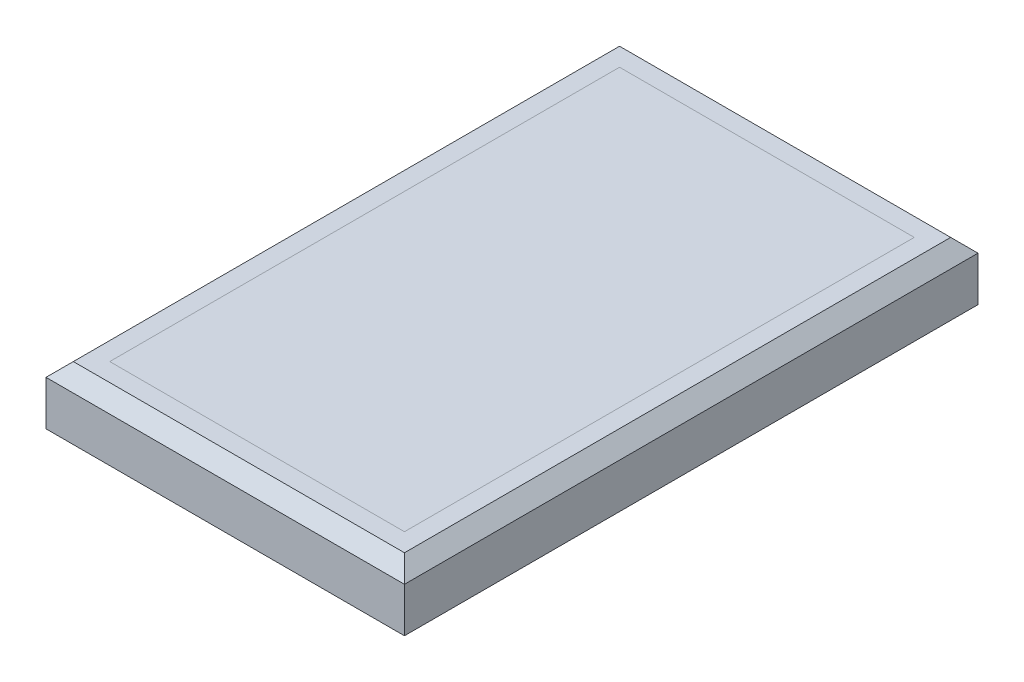
SolidWorks part; units mm, degrees
ref_plane "Front" through (0, 0, 0) normal (0, 0, 1) x (1, 0, 0)
ref_plane "Top" through (0, 0, 0) normal (0, 1, 0) x (1, 0, 0)
ref_plane "Right" through (0, 0, 0) normal (1, 0, 0) x (0, 0, -1)
sketch "Sketch1" plane through (0, 0, 0) normal (0, 1, 0) x (1, 0, 0)
  line L0 (-125, 200) -> (125, -200) construction
  line L1 (-125, 200) -> (125, 200)
  line L2 (-125, 200) -> (-125, -200)
  line L3 (-125, -200) -> (125, -200)
  line L4 (125, 200) -> (125, -200)
  dimension "D1" = 250
  dimension "D2" = 400
extrude "Boss-Extrude1" add sketch "Sketch1" along normal blind 40.64
sketch "Sketch2" plane through (0, 40.64, 0) normal (0, 1, 0) x (1, 0, 0)
  line L8 (-102.775, 177.775) -> (-102.775, -177.775)
  line L9 (-102.775, -177.775) -> (102.775, -177.775)
  line L10 (102.775, -177.775) -> (102.775, 177.775)
  line L11 (102.775, 177.775) -> (-102.775, 177.775)
  line L12 (-102.775, 177.775) -> (-102.775, -177.775)
  line L13 (-102.775, -177.775) -> (102.775, -177.775)
  line L14 (102.775, -177.775) -> (102.775, 177.775)
  line L15 (102.775, 177.775) -> (-102.775, 177.775)
  dimension "D1" = 22.225
extrude "Cut-Extrude1" cut sketch "Sketch2" against normal blind 38.1
chamfer "Chamfer1" distance 9.525 angle 45 4 edges at (0, 40.64, -200) (125, 40.64, 0) (0, 40.64, 200) (-125, 40.64, 0)
ref_plane "Plane1" through (0, 37.465, 0) normal (0, 1, 0) x (1, 0, 0)
sketch "Sketch3" plane through (0, 37.465, 0) normal (0, 1, 0) x (1, 0, 0)
  line L0 (0, 177.775) -> (0, -177.775) construction
  line L1 (102.775, 177.775) -> (-102.775, 177.775) construction
  line L2 (-102.775, -177.775) -> (102.775, -177.775) construction
  line L3 (102.775, -177.775) -> (102.775, 177.775) construction
  line L4 (-102.775, 177.775) -> (-102.775, -177.775) construction
  line L5 (-102.775, -177.775) -> (102.775, -177.775)
  line L6 (102.775, -177.775) -> (102.775, 177.775)
  line L7 (-102.775, 177.775) -> (-102.775, -177.775)
  line L8 (102.775, 177.775) -> (-102.775, 177.775)
extrude "Boss-Extrude2" add sketch "Sketch3" against normal blind 3.175 separate body
sketch "Sketch4" plane through (0, 37.465, 0) normal (0, 1, 0) x (1, 0, 0)
  line L0 (0, 177.775) -> (0, -177.775) construction
  line L1 (102.775, 177.775) -> (-102.775, 177.775) construction
  line L2 (-102.775, -177.775) -> (102.775, -177.775) construction
  line L3 (1.5875, 177.775) -> (1.5875, -177.775)
  line L4 (-1.5875, 177.775) -> (-1.5875, -177.775)
  line L5 (71.1625, 177.775) -> (67.9875, 177.775)
  line L6 (-71.1625, -177.775) -> (-67.9875, -177.775)
  line L7 (36.375, 177.775) -> (36.375, -177.775)
  line L8 (33.2, 177.775) -> (33.2, -177.775)
  line L9 (71.1625, 177.775) -> (71.1625, -177.775)
  line L10 (67.9875, 177.775) -> (67.9875, -177.775)
  line L11 (-33.2, 177.775) -> (-33.2, -177.775)
  line L12 (-36.375, 177.775) -> (-36.375, -177.775)
  line L13 (-67.9875, 177.775) -> (-67.9875, -177.775)
  line L14 (-71.1625, 177.775) -> (-71.1625, -177.775)
  line L15 (102.775, 177.775) -> (-102.775, 177.775) construction
  line L16 (1.5875, 0) -> (33.2, 0) construction
  line L17 (36.375, 0) -> (67.9875, 0) construction
  line L18 (71.1625, 0) -> (102.775, 0) construction
  line L19 (102.775, -177.775) -> (102.775, 177.775) construction
  line L20 (-1.5875, 0) -> (-33.2, 0) construction
  line L21 (-36.375, 0) -> (-67.9875, 0) construction
  line L22 (-71.1625, 0) -> (-102.775, 0) construction
  line L23 (-102.775, 177.775) -> (-102.775, -177.775) construction
  line L24 (36.375, 177.775) -> (33.2, 177.775)
  line L25 (1.5875, 177.775) -> (-1.5875, 177.775)
  line L26 (-33.2, 177.775) -> (-36.375, 177.775)
  line L27 (-67.9875, 177.775) -> (-71.1625, 177.775)
  line L28 (67.9875, -177.775) -> (71.1625, -177.775)
  line L29 (33.2, -177.775) -> (36.375, -177.775)
  line L30 (-1.5875, -177.775) -> (1.5875, -177.775)
  line L31 (-36.375, -177.775) -> (-33.2, -177.775)
  dimension "D1" = 3.175
extrude "Cut-Extrude2" cut sketch "Sketch4" against normal blind 7.62
sketch "Sketch5" plane through (0, 37.465, 0) normal (0, 1, 0) x (1, 0, 0)
  line L0 (-102.775, 0) -> (102.775, 0) construction
  line L1 (-102.775, 177.775) -> (-102.775, -177.775) construction
  line L2 (102.775, -177.775) -> (102.775, 177.775) construction
  line L3 (-102.775, 1.5875) -> (102.775, 1.5875)
  line L4 (102.775, -177.775) -> (102.775, 177.775) construction
  line L5 (-102.775, 177.775) -> (-102.775, -177.775) construction
  line L6 (-102.775, -1.5875) -> (102.775, -1.5875)
  line L7 (-102.775, -34.285) -> (102.775, -34.285)
  line L8 (-102.775, -37.46) -> (102.775, -37.46)
  line L9 (-102.775, -70.1575) -> (102.775, -70.1575)
  line L10 (-102.775, -73.3325) -> (102.775, -73.3325)
  line L11 (-102.775, -106.03) -> (102.775, -106.03)
  line L12 (-102.775, -109.205) -> (102.775, -109.205)
  line L13 (-102.775, -141.9025) -> (102.775, -141.9025)
  line L14 (-102.775, -145.0775) -> (102.775, -145.0775)
  line L15 (-102.775, 37.46) -> (102.775, 37.46)
  line L16 (-102.775, 34.285) -> (102.775, 34.285)
  line L17 (-102.775, 73.3325) -> (102.775, 73.3325)
  line L18 (-102.775, 70.1575) -> (102.775, 70.1575)
  line L19 (-102.775, 109.205) -> (102.775, 109.205)
  line L20 (-102.775, 106.03) -> (102.775, 106.03)
  line L21 (-102.775, 145.0775) -> (102.775, 145.0775)
  line L22 (-102.775, 141.9025) -> (102.775, 141.9025)
  line L23 (102.775, -145.0775) -> (102.775, -141.9025)
  line L24 (-102.775, 145.0775) -> (-102.775, 141.9025)
  line L25 (-102.775, 109.205) -> (-102.775, 106.03)
  line L26 (102.775, 141.9025) -> (102.775, 145.0775)
  line L27 (102.775, 106.03) -> (102.775, 109.205)
  line L28 (-102.775, 73.3325) -> (-102.775, 70.1575)
  line L29 (-102.775, 37.46) -> (-102.775, 34.285)
  line L30 (102.775, 70.1575) -> (102.775, 73.3325)
  line L31 (102.775, 34.285) -> (102.775, 37.46)
  line L32 (-102.775, 1.5875) -> (-102.775, -1.5875)
  line L33 (-102.775, -70.1575) -> (-102.775, -73.3325)
  line L34 (102.775, -37.46) -> (102.775, -34.285)
  line L35 (-102.775, -106.03) -> (-102.775, -109.205)
  line L36 (102.775, -73.3325) -> (102.775, -70.1575)
  line L37 (102.775, -109.205) -> (102.775, -106.03)
  line L38 (-102.775, -141.9025) -> (-102.775, -145.0775)
  line L39 (102.775, 1.5875) -> (102.775, -1.5875)
  line L40 (0, -1.5875) -> (0, -34.285) construction
  line L41 (-102.775, -34.285) -> (-102.775, -37.46)
  line L42 (0, -37.46) -> (0, -70.1575) construction
  line L43 (0, -73.3325) -> (0, -106.03) construction
  line L44 (0, -109.205) -> (0, -141.9025) construction
  line L45 (0, -145.0775) -> (0, -177.775) construction
  line L46 (-102.775, -177.775) -> (102.775, -177.775) construction
  line L47 (0, 1.5875) -> (0, 34.285) construction
  line L48 (0, 37.46) -> (0, 70.1575) construction
  line L49 (0, 73.3325) -> (0, 106.03) construction
  line L50 (0, 109.205) -> (0, 141.9025) construction
  line L51 (0, 145.0775) -> (0, 177.775) construction
  line L52 (102.775, 177.775) -> (-102.775, 177.775) construction
  dimension "D1" = 3.175
extrude "Cut-Extrude3" cut sketch "Sketch5" against normal blind 7.62
sketch "Sketch6" plane through (0, 37.465, 0) normal (0, 1, 0) x (1, 0, 0)
  line L0 (-71.1625, -109.205) -> (-102.775, -109.205) construction
  line L1 (-102.775, -141.9025) -> (-102.775, -145.0775)
  line L2 (-102.775, -141.9025) -> (-71.1625, -141.9025) construction
  line L3 (-71.1625, -141.9025) -> (-71.1625, -109.205) construction
  line L4 (-71.1625, -145.0775) -> (-102.775, -145.0775) construction
  line L5 (-102.775, -106.03) -> (-102.775, -109.205)
  line L6 (-102.775, -70.1575) -> (-102.775, -73.3325)
  line L7 (-71.1625, -177.775) -> (-71.1625, -145.0775) construction
  line L8 (-36.375, -145.0775) -> (-67.9875, -145.0775) construction
  line L9 (-67.9875, -145.0775) -> (-67.9875, -177.775) construction
  line L10 (-102.775, -34.285) -> (-102.775, -37.46)
  line L11 (-36.375, -177.775) -> (-36.375, -145.0775) construction
  line L12 (-36.375, -109.205) -> (-67.9875, -109.205) construction
  line L13 (-67.9875, -109.205) -> (-67.9875, -141.9025) construction
  line L14 (-67.9875, -141.9025) -> (-36.375, -141.9025) construction
  line L15 (-36.375, -141.9025) -> (-36.375, -109.205) construction
  line L16 (-1.5875, -109.205) -> (-33.2, -109.205) construction
  line L17 (-33.2, -109.205) -> (-33.2, -141.9025) construction
  line L18 (-33.2, -141.9025) -> (-1.5875, -141.9025) construction
  line L19 (-1.5875, -141.9025) -> (-1.5875, -109.205) construction
  line L20 (-1.5875, -145.0775) -> (-33.2, -145.0775) construction
  line L21 (-33.2, -145.0775) -> (-33.2, -177.775) construction
  line L22 (-102.775, 1.5875) -> (-102.775, -1.5875)
  line L23 (-1.5875, -177.775) -> (-1.5875, -145.0775) construction
  line L24 (33.2, -145.0775) -> (1.5875, -145.0775) construction
  line L25 (1.5875, -145.0775) -> (1.5875, -177.775) construction
  line L26 (-102.775, 37.46) -> (-102.775, 34.285)
  line L27 (33.2, -177.775) -> (33.2, -145.0775) construction
  line L28 (33.2, -109.205) -> (1.5875, -109.205) construction
  line L29 (1.5875, -109.205) -> (1.5875, -141.9025) construction
  line L30 (1.5875, -141.9025) -> (33.2, -141.9025) construction
  line L31 (33.2, -141.9025) -> (33.2, -109.205) construction
  line L32 (67.9875, -109.205) -> (36.375, -109.205) construction
  line L33 (36.375, -109.205) -> (36.375, -141.9025) construction
  line L34 (36.375, -141.9025) -> (67.9875, -141.9025) construction
  line L35 (67.9875, -141.9025) -> (67.9875, -109.205) construction
  line L36 (67.9875, -145.0775) -> (36.375, -145.0775) construction
  line L37 (36.375, -145.0775) -> (36.375, -177.775) construction
  line L38 (-102.775, 73.3325) -> (-102.775, 70.1575)
  line L39 (67.9875, -177.775) -> (67.9875, -145.0775) construction
  line L40 (102.775, -145.0775) -> (71.1625, -145.0775) construction
  line L41 (71.1625, -145.0775) -> (71.1625, -177.775) construction
  line L42 (-102.775, 109.205) -> (-102.775, 106.03)
  line L43 (-67.9875, 177.775) -> (-71.1625, 177.775)
  line L44 (102.775, -109.205) -> (71.1625, -109.205) construction
  line L45 (71.1625, -109.205) -> (71.1625, -141.9025) construction
  line L46 (71.1625, -141.9025) -> (102.775, -141.9025) construction
  line L47 (-33.2, 177.775) -> (-36.375, 177.775)
  line L48 (102.775, -73.3325) -> (71.1625, -73.3325) construction
  line L49 (71.1625, -73.3325) -> (71.1625, -106.03) construction
  line L50 (71.1625, -106.03) -> (102.775, -106.03) construction
  line L51 (1.5875, 177.775) -> (-1.5875, 177.775)
  line L52 (67.9875, -73.3325) -> (36.375, -73.3325) construction
  line L53 (36.375, -73.3325) -> (36.375, -106.03) construction
  line L54 (36.375, -106.03) -> (67.9875, -106.03) construction
  line L55 (67.9875, -106.03) -> (67.9875, -73.3325) construction
  line L56 (33.2, -73.3325) -> (1.5875, -73.3325) construction
  line L57 (1.5875, -73.3325) -> (1.5875, -106.03) construction
  line L58 (1.5875, -106.03) -> (33.2, -106.03) construction
  line L59 (33.2, -106.03) -> (33.2, -73.3325) construction
  line L60 (-1.5875, -73.3325) -> (-33.2, -73.3325) construction
  line L61 (-33.2, -73.3325) -> (-33.2, -106.03) construction
  line L62 (-33.2, -106.03) -> (-1.5875, -106.03) construction
  line L63 (-1.5875, -106.03) -> (-1.5875, -73.3325) construction
  line L64 (-36.375, -73.3325) -> (-67.9875, -73.3325) construction
  line L65 (-67.9875, -73.3325) -> (-67.9875, -106.03) construction
  line L66 (-67.9875, -106.03) -> (-36.375, -106.03) construction
  line L67 (-36.375, -106.03) -> (-36.375, -73.3325) construction
  line L68 (-71.1625, -73.3325) -> (-102.775, -73.3325) construction
  line L69 (36.375, 177.775) -> (33.2, 177.775)
  line L70 (-102.775, -106.03) -> (-71.1625, -106.03) construction
  line L71 (-71.1625, -106.03) -> (-71.1625, -73.3325) construction
  line L72 (-71.1625, -37.46) -> (-102.775, -37.46) construction
  line L73 (102.775, 141.9025) -> (102.775, 145.0775)
  line L74 (-102.775, -70.1575) -> (-71.1625, -70.1575) construction
  line L75 (-71.1625, -70.1575) -> (-71.1625, -37.46) construction
  line L76 (-36.375, -37.46) -> (-67.9875, -37.46) construction
  line L77 (-67.9875, -37.46) -> (-67.9875, -70.1575) construction
  line L78 (-67.9875, -70.1575) -> (-36.375, -70.1575) construction
  line L79 (-36.375, -70.1575) -> (-36.375, -37.46) construction
  line L80 (-1.5875, -37.46) -> (-33.2, -37.46) construction
  line L81 (-33.2, -37.46) -> (-33.2, -70.1575) construction
  line L82 (-33.2, -70.1575) -> (-1.5875, -70.1575) construction
  line L83 (-1.5875, -70.1575) -> (-1.5875, -37.46) construction
  line L84 (33.2, -37.46) -> (1.5875, -37.46) construction
  line L85 (1.5875, -37.46) -> (1.5875, -70.1575) construction
  line L86 (1.5875, -70.1575) -> (33.2, -70.1575) construction
  line L87 (33.2, -70.1575) -> (33.2, -37.46) construction
  line L88 (67.9875, -37.46) -> (36.375, -37.46) construction
  line L89 (36.375, -37.46) -> (36.375, -70.1575) construction
  line L90 (36.375, -70.1575) -> (67.9875, -70.1575) construction
  line L91 (67.9875, -70.1575) -> (67.9875, -37.46) construction
  line L92 (102.775, -37.46) -> (71.1625, -37.46) construction
  line L93 (71.1625, -37.46) -> (71.1625, -70.1575) construction
  line L94 (71.1625, -70.1575) -> (102.775, -70.1575) construction
  line L95 (102.775, 106.03) -> (102.775, 109.205)
  line L96 (102.775, -1.5875) -> (71.1625, -1.5875) construction
  line L97 (71.1625, -1.5875) -> (71.1625, -34.285) construction
  line L98 (71.1625, -34.285) -> (102.775, -34.285) construction
  line L99 (102.775, 70.1575) -> (102.775, 73.3325)
  line L100 (67.9875, -1.5875) -> (36.375, -1.5875) construction
  line L101 (36.375, -1.5875) -> (36.375, -34.285) construction
  line L102 (36.375, -34.285) -> (67.9875, -34.285) construction
  line L103 (67.9875, -34.285) -> (67.9875, -1.5875) construction
  line L104 (33.2, -1.5875) -> (1.5875, -1.5875) construction
  line L105 (1.5875, -1.5875) -> (1.5875, -34.285) construction
  line L106 (1.5875, -34.285) -> (33.2, -34.285) construction
  line L107 (33.2, -34.285) -> (33.2, -1.5875) construction
  line L108 (-1.5875, -1.5875) -> (-33.2, -1.5875) construction
  line L109 (-33.2, -1.5875) -> (-33.2, -34.285) construction
  line L110 (-33.2, -34.285) -> (-1.5875, -34.285) construction
  line L111 (-1.5875, -34.285) -> (-1.5875, -1.5875) construction
  line L112 (-36.375, -1.5875) -> (-67.9875, -1.5875) construction
  line L113 (-67.9875, -1.5875) -> (-67.9875, -34.285) construction
  line L114 (-67.9875, -34.285) -> (-36.375, -34.285) construction
  line L115 (-36.375, -34.285) -> (-36.375, -1.5875) construction
  line L116 (-71.1625, -1.5875) -> (-102.775, -1.5875) construction
  line L117 (102.775, 34.285) -> (102.775, 37.46)
  line L118 (-102.775, -34.285) -> (-71.1625, -34.285) construction
  line L119 (-71.1625, -34.285) -> (-71.1625, -1.5875) construction
  line L120 (-102.775, 1.5875) -> (-71.1625, 1.5875) construction
  line L121 (-71.1625, 1.5875) -> (-71.1625, 34.285) construction
  line L122 (-71.1625, 34.285) -> (-102.775, 34.285) construction
  line L123 (102.775, -1.5875) -> (102.775, 1.5875)
  line L124 (-67.9875, 1.5875) -> (-36.375, 1.5875) construction
  line L125 (-36.375, 1.5875) -> (-36.375, 34.285) construction
  line L126 (-36.375, 34.285) -> (-67.9875, 34.285) construction
  line L127 (-67.9875, 34.285) -> (-67.9875, 1.5875) construction
  line L128 (-33.2, 1.5875) -> (-1.5875, 1.5875) construction
  line L129 (-1.5875, 1.5875) -> (-1.5875, 34.285) construction
  line L130 (-1.5875, 34.285) -> (-33.2, 34.285) construction
  line L131 (-33.2, 34.285) -> (-33.2, 1.5875) construction
  line L132 (1.5875, 1.5875) -> (33.2, 1.5875) construction
  line L133 (33.2, 1.5875) -> (33.2, 34.285) construction
  line L134 (33.2, 34.285) -> (1.5875, 34.285) construction
  line L135 (1.5875, 34.285) -> (1.5875, 1.5875) construction
  line L136 (36.375, 1.5875) -> (67.9875, 1.5875) construction
  line L137 (67.9875, 1.5875) -> (67.9875, 34.285) construction
  line L138 (67.9875, 34.285) -> (36.375, 34.285) construction
  line L139 (36.375, 34.285) -> (36.375, 1.5875) construction
  line L140 (71.1625, 1.5875) -> (102.775, 1.5875) construction
  line L142 (102.775, 34.285) -> (71.1625, 34.285) construction
  line L143 (71.1625, 34.285) -> (71.1625, 1.5875) construction
  line L144 (71.1625, 37.46) -> (102.775, 37.46) construction
  line L146 (102.775, 70.1575) -> (71.1625, 70.1575) construction
  line L147 (71.1625, 70.1575) -> (71.1625, 37.46) construction
  line L148 (71.1625, 73.3325) -> (102.775, 73.3325) construction
  line L150 (102.775, 106.03) -> (71.1625, 106.03) construction
  line L151 (71.1625, 106.03) -> (71.1625, 73.3325) construction
  line L152 (71.1625, 109.205) -> (102.775, 109.205) construction
  line L154 (102.775, 141.9025) -> (71.1625, 141.9025) construction
  line L155 (71.1625, 141.9025) -> (71.1625, 109.205) construction
  line L156 (71.1625, 145.0775) -> (102.775, 145.0775) construction
  line L159 (71.1625, 177.775) -> (71.1625, 145.0775) construction
  line L160 (36.375, 145.0775) -> (67.9875, 145.0775) construction
  line L161 (67.9875, 145.0775) -> (67.9875, 177.775) construction
  line L163 (36.375, 177.775) -> (36.375, 145.0775) construction
  line L164 (36.375, 109.205) -> (67.9875, 109.205) construction
  line L165 (67.9875, 109.205) -> (67.9875, 141.9025) construction
  line L166 (67.9875, 141.9025) -> (36.375, 141.9025) construction
  line L167 (36.375, 141.9025) -> (36.375, 109.205) construction
  line L168 (36.375, 73.3325) -> (67.9875, 73.3325) construction
  line L169 (67.9875, 73.3325) -> (67.9875, 106.03) construction
  line L170 (67.9875, 106.03) -> (36.375, 106.03) construction
  line L171 (36.375, 106.03) -> (36.375, 73.3325) construction
  line L172 (36.375, 37.46) -> (67.9875, 37.46) construction
  line L173 (67.9875, 37.46) -> (67.9875, 70.1575) construction
  line L174 (67.9875, 70.1575) -> (36.375, 70.1575) construction
  line L175 (36.375, 70.1575) -> (36.375, 37.46) construction
  line L176 (1.5875, 37.46) -> (33.2, 37.46) construction
  line L177 (33.2, 37.46) -> (33.2, 70.1575) construction
  line L178 (33.2, 70.1575) -> (1.5875, 70.1575) construction
  line L179 (1.5875, 70.1575) -> (1.5875, 37.46) construction
  line L180 (1.5875, 73.3325) -> (33.2, 73.3325) construction
  line L181 (33.2, 73.3325) -> (33.2, 106.03) construction
  line L182 (33.2, 106.03) -> (1.5875, 106.03) construction
  line L183 (1.5875, 106.03) -> (1.5875, 73.3325) construction
  line L184 (1.5875, 109.205) -> (33.2, 109.205) construction
  line L185 (33.2, 109.205) -> (33.2, 141.9025) construction
  line L186 (33.2, 141.9025) -> (1.5875, 141.9025) construction
  line L187 (1.5875, 141.9025) -> (1.5875, 109.205) construction
  line L188 (1.5875, 145.0775) -> (33.2, 145.0775) construction
  line L189 (33.2, 145.0775) -> (33.2, 177.775) construction
  line L191 (1.5875, 177.775) -> (1.5875, 145.0775) construction
  line L192 (-33.2, 145.0775) -> (-1.5875, 145.0775) construction
  line L193 (-1.5875, 145.0775) -> (-1.5875, 177.775) construction
  line L195 (-33.2, 177.775) -> (-33.2, 145.0775) construction
  line L196 (-33.2, 109.205) -> (-1.5875, 109.205) construction
  line L197 (-1.5875, 109.205) -> (-1.5875, 141.9025) construction
  line L198 (-1.5875, 141.9025) -> (-33.2, 141.9025) construction
  line L199 (-33.2, 141.9025) -> (-33.2, 109.205) construction
  line L200 (-33.2, 73.3325) -> (-1.5875, 73.3325) construction
  line L201 (-1.5875, 73.3325) -> (-1.5875, 106.03) construction
  line L202 (-1.5875, 106.03) -> (-33.2, 106.03) construction
  line L203 (-33.2, 106.03) -> (-33.2, 73.3325) construction
  line L204 (-33.2, 37.46) -> (-1.5875, 37.46) construction
  line L205 (-1.5875, 37.46) -> (-1.5875, 70.1575) construction
  line L206 (-1.5875, 70.1575) -> (-33.2, 70.1575) construction
  line L207 (-33.2, 70.1575) -> (-33.2, 37.46) construction
  line L208 (-67.9875, 37.46) -> (-36.375, 37.46) construction
  line L209 (-36.375, 37.46) -> (-36.375, 70.1575) construction
  line L210 (-36.375, 70.1575) -> (-67.9875, 70.1575) construction
  line L211 (-67.9875, 70.1575) -> (-67.9875, 37.46) construction
  line L212 (-67.9875, 109.205) -> (-36.375, 109.205) construction
  line L213 (-36.375, 109.205) -> (-36.375, 141.9025) construction
  line L214 (-36.375, 141.9025) -> (-67.9875, 141.9025) construction
  line L215 (-67.9875, 141.9025) -> (-67.9875, 109.205) construction
  line L216 (-67.9875, 145.0775) -> (-36.375, 145.0775) construction
  line L217 (-36.375, 145.0775) -> (-36.375, 177.775) construction
  line L219 (-67.9875, 177.775) -> (-67.9875, 145.0775) construction
  line L220 (-102.775, 145.0775) -> (-71.1625, 145.0775) construction
  line L221 (-71.1625, 145.0775) -> (-71.1625, 177.775) construction
  line L224 (-102.775, 109.205) -> (-71.1625, 109.205) construction
  line L225 (-71.1625, 109.205) -> (-71.1625, 141.9025) construction
  line L226 (-71.1625, 141.9025) -> (-102.775, 141.9025) construction
  line L228 (-102.775, 73.3325) -> (-71.1625, 73.3325) construction
  line L229 (-71.1625, 73.3325) -> (-71.1625, 106.03) construction
  line L230 (-71.1625, 106.03) -> (-102.775, 106.03) construction
  line L232 (-102.775, 37.46) -> (-71.1625, 37.46) construction
  line L233 (-71.1625, 37.46) -> (-71.1625, 70.1575) construction
  line L234 (-71.1625, 70.1575) -> (-102.775, 70.1575) construction
  line L236 (-67.9875, 73.3325) -> (-36.375, 73.3325) construction
  line L237 (-36.375, 73.3325) -> (-36.375, 106.03) construction
  line L238 (-36.375, 106.03) -> (-67.9875, 106.03) construction
  line L239 (-67.9875, 106.03) -> (-67.9875, 73.3325) construction
  line L240 (-71.1625, -109.205) -> (-102.775, -109.205)
  line L241 (102.775, 177.775) -> (-102.775, 177.775) construction
  line L242 (-102.775, -141.9025) -> (-71.1625, -141.9025)
  line L243 (-71.1625, -141.9025) -> (-71.1625, -109.205)
  line L244 (-71.1625, -145.0775) -> (-102.775, -145.0775)
  line L245 (71.1625, 177.775) -> (67.9875, 177.775)
  line L246 (102.775, -177.775) -> (102.775, 177.775) construction
  line L247 (-71.1625, -177.775) -> (-71.1625, -145.0775)
  line L248 (-36.375, -145.0775) -> (-67.9875, -145.0775)
  line L249 (-67.9875, -145.0775) -> (-67.9875, -177.775)
  line L250 (102.775, -145.0775) -> (102.775, -141.9025)
  line L251 (-36.375, -177.775) -> (-36.375, -145.0775)
  line L252 (-36.375, -109.205) -> (-67.9875, -109.205)
  line L253 (-67.9875, -109.205) -> (-67.9875, -141.9025)
  line L254 (-67.9875, -141.9025) -> (-36.375, -141.9025)
  line L255 (-36.375, -141.9025) -> (-36.375, -109.205)
  line L256 (-1.5875, -109.205) -> (-33.2, -109.205)
  line L257 (-33.2, -109.205) -> (-33.2, -141.9025)
  line L258 (-33.2, -141.9025) -> (-1.5875, -141.9025)
  line L259 (-1.5875, -141.9025) -> (-1.5875, -109.205)
  line L260 (-1.5875, -145.0775) -> (-33.2, -145.0775)
  line L261 (-33.2, -145.0775) -> (-33.2, -177.775)
  line L262 (-102.775, 177.775) -> (-102.775, -177.775) construction
  line L263 (-1.5875, -177.775) -> (-1.5875, -145.0775)
  line L264 (33.2, -145.0775) -> (1.5875, -145.0775)
  line L265 (1.5875, -145.0775) -> (1.5875, -177.775)
  line L266 (-102.775, 145.0775) -> (-102.775, 141.9025)
  line L267 (33.2, -177.775) -> (33.2, -145.0775)
  line L268 (33.2, -109.205) -> (1.5875, -109.205)
  line L269 (1.5875, -109.205) -> (1.5875, -141.9025)
  line L270 (1.5875, -141.9025) -> (33.2, -141.9025)
  line L271 (33.2, -141.9025) -> (33.2, -109.205)
  line L272 (67.9875, -109.205) -> (36.375, -109.205)
  line L273 (36.375, -109.205) -> (36.375, -141.9025)
  line L274 (36.375, -141.9025) -> (67.9875, -141.9025)
  line L275 (67.9875, -141.9025) -> (67.9875, -109.205)
  line L276 (67.9875, -145.0775) -> (36.375, -145.0775)
  line L277 (36.375, -145.0775) -> (36.375, -177.775)
  line L278 (-102.775, -177.775) -> (102.775, -177.775) construction
  line L279 (67.9875, -177.775) -> (67.9875, -145.0775)
  line L280 (102.775, -145.0775) -> (71.1625, -145.0775)
  line L281 (71.1625, -145.0775) -> (71.1625, -177.775)
  line L282 (-71.1625, -177.775) -> (-67.9875, -177.775)
  line L283 (67.9875, -177.775) -> (71.1625, -177.775)
  line L284 (102.775, -109.205) -> (71.1625, -109.205)
  line L285 (71.1625, -109.205) -> (71.1625, -141.9025)
  line L286 (71.1625, -141.9025) -> (102.775, -141.9025)
  line L287 (33.2, -177.775) -> (36.375, -177.775)
  line L288 (102.775, -73.3325) -> (71.1625, -73.3325)
  line L289 (71.1625, -73.3325) -> (71.1625, -106.03)
  line L290 (71.1625, -106.03) -> (102.775, -106.03)
  line L291 (-1.5875, -177.775) -> (1.5875, -177.775)
  line L292 (67.9875, -73.3325) -> (36.375, -73.3325)
  line L293 (36.375, -73.3325) -> (36.375, -106.03)
  line L294 (36.375, -106.03) -> (67.9875, -106.03)
  line L295 (67.9875, -106.03) -> (67.9875, -73.3325)
  line L296 (33.2, -73.3325) -> (1.5875, -73.3325)
  line L297 (1.5875, -73.3325) -> (1.5875, -106.03)
  line L298 (1.5875, -106.03) -> (33.2, -106.03)
  line L299 (33.2, -106.03) -> (33.2, -73.3325)
  line L300 (-1.5875, -73.3325) -> (-33.2, -73.3325)
  line L301 (-33.2, -73.3325) -> (-33.2, -106.03)
  line L302 (-33.2, -106.03) -> (-1.5875, -106.03)
  line L303 (-1.5875, -106.03) -> (-1.5875, -73.3325)
  line L304 (-36.375, -73.3325) -> (-67.9875, -73.3325)
  line L305 (-67.9875, -73.3325) -> (-67.9875, -106.03)
  line L306 (-67.9875, -106.03) -> (-36.375, -106.03)
  line L307 (-36.375, -106.03) -> (-36.375, -73.3325)
  line L308 (-71.1625, -73.3325) -> (-102.775, -73.3325)
  line L309 (-36.375, -177.775) -> (-33.2, -177.775)
  line L310 (-102.775, -106.03) -> (-71.1625, -106.03)
  line L311 (-71.1625, -106.03) -> (-71.1625, -73.3325)
  line L312 (-71.1625, -37.46) -> (-102.775, -37.46)
  line L313 (102.775, -109.205) -> (102.775, -106.03)
  line L314 (-102.775, -70.1575) -> (-71.1625, -70.1575)
  line L315 (-71.1625, -70.1575) -> (-71.1625, -37.46)
  line L316 (-36.375, -37.46) -> (-67.9875, -37.46)
  line L317 (-67.9875, -37.46) -> (-67.9875, -70.1575)
  line L318 (-67.9875, -70.1575) -> (-36.375, -70.1575)
  line L319 (-36.375, -70.1575) -> (-36.375, -37.46)
  line L320 (-1.5875, -37.46) -> (-33.2, -37.46)
  line L321 (-33.2, -37.46) -> (-33.2, -70.1575)
  line L322 (-33.2, -70.1575) -> (-1.5875, -70.1575)
  line L323 (-1.5875, -70.1575) -> (-1.5875, -37.46)
  line L324 (33.2, -37.46) -> (1.5875, -37.46)
  line L325 (1.5875, -37.46) -> (1.5875, -70.1575)
  line L326 (1.5875, -70.1575) -> (33.2, -70.1575)
  line L327 (33.2, -70.1575) -> (33.2, -37.46)
  line L328 (67.9875, -37.46) -> (36.375, -37.46)
  line L329 (36.375, -37.46) -> (36.375, -70.1575)
  line L330 (36.375, -70.1575) -> (67.9875, -70.1575)
  line L331 (67.9875, -70.1575) -> (67.9875, -37.46)
  line L332 (102.775, -37.46) -> (71.1625, -37.46)
  line L333 (71.1625, -37.46) -> (71.1625, -70.1575)
  line L334 (71.1625, -70.1575) -> (102.775, -70.1575)
  line L335 (102.775, -73.3325) -> (102.775, -70.1575)
  line L336 (102.775, -1.5875) -> (71.1625, -1.5875)
  line L337 (71.1625, -1.5875) -> (71.1625, -34.285)
  line L338 (71.1625, -34.285) -> (102.775, -34.285)
  line L339 (102.775, -37.46) -> (102.775, -34.285)
  line L340 (67.9875, -1.5875) -> (36.375, -1.5875)
  line L341 (36.375, -1.5875) -> (36.375, -34.285)
  line L342 (36.375, -34.285) -> (67.9875, -34.285)
  line L343 (67.9875, -34.285) -> (67.9875, -1.5875)
  line L344 (33.2, -1.5875) -> (1.5875, -1.5875)
  line L345 (1.5875, -1.5875) -> (1.5875, -34.285)
  line L346 (1.5875, -34.285) -> (33.2, -34.285)
  line L347 (33.2, -34.285) -> (33.2, -1.5875)
  line L348 (-1.5875, -1.5875) -> (-33.2, -1.5875)
  line L349 (-33.2, -1.5875) -> (-33.2, -34.285)
  line L350 (-33.2, -34.285) -> (-1.5875, -34.285)
  line L351 (-1.5875, -34.285) -> (-1.5875, -1.5875)
  line L352 (-36.375, -1.5875) -> (-67.9875, -1.5875)
  line L353 (-67.9875, -1.5875) -> (-67.9875, -34.285)
  line L354 (-67.9875, -34.285) -> (-36.375, -34.285)
  line L355 (-36.375, -34.285) -> (-36.375, -1.5875)
  line L356 (-71.1625, -1.5875) -> (-102.775, -1.5875)
  line L358 (-102.775, -34.285) -> (-71.1625, -34.285)
  line L359 (-71.1625, -34.285) -> (-71.1625, -1.5875)
  line L360 (-102.775, 1.5875) -> (-71.1625, 1.5875)
  line L361 (-71.1625, 1.5875) -> (-71.1625, 34.285)
  line L362 (-71.1625, 34.285) -> (-102.775, 34.285)
  line L364 (-67.9875, 1.5875) -> (-36.375, 1.5875)
  line L365 (-36.375, 1.5875) -> (-36.375, 34.285)
  line L366 (-36.375, 34.285) -> (-67.9875, 34.285)
  line L367 (-67.9875, 34.285) -> (-67.9875, 1.5875)
  line L368 (-33.2, 1.5875) -> (-1.5875, 1.5875)
  line L369 (-1.5875, 1.5875) -> (-1.5875, 34.285)
  line L370 (-1.5875, 34.285) -> (-33.2, 34.285)
  line L371 (-33.2, 34.285) -> (-33.2, 1.5875)
  line L372 (1.5875, 1.5875) -> (33.2, 1.5875)
  line L373 (33.2, 1.5875) -> (33.2, 34.285)
  line L374 (33.2, 34.285) -> (1.5875, 34.285)
  line L375 (1.5875, 34.285) -> (1.5875, 1.5875)
  line L376 (36.375, 1.5875) -> (67.9875, 1.5875)
  line L377 (67.9875, 1.5875) -> (67.9875, 34.285)
  line L378 (67.9875, 34.285) -> (36.375, 34.285)
  line L379 (36.375, 34.285) -> (36.375, 1.5875)
  line L380 (71.1625, 1.5875) -> (102.775, 1.5875)
  line L382 (102.775, 34.285) -> (71.1625, 34.285)
  line L383 (71.1625, 34.285) -> (71.1625, 1.5875)
  line L384 (71.1625, 37.46) -> (102.775, 37.46)
  line L386 (102.775, 70.1575) -> (71.1625, 70.1575)
  line L387 (71.1625, 70.1575) -> (71.1625, 37.46)
  line L388 (71.1625, 73.3325) -> (102.775, 73.3325)
  line L390 (102.775, 106.03) -> (71.1625, 106.03)
  line L391 (71.1625, 106.03) -> (71.1625, 73.3325)
  line L392 (71.1625, 109.205) -> (102.775, 109.205)
  line L394 (102.775, 141.9025) -> (71.1625, 141.9025)
  line L395 (71.1625, 141.9025) -> (71.1625, 109.205)
  line L396 (71.1625, 145.0775) -> (102.775, 145.0775)
  line L399 (71.1625, 177.775) -> (71.1625, 145.0775)
  line L400 (36.375, 145.0775) -> (67.9875, 145.0775)
  line L401 (67.9875, 145.0775) -> (67.9875, 177.775)
  line L403 (36.375, 177.775) -> (36.375, 145.0775)
  line L404 (36.375, 109.205) -> (67.9875, 109.205)
  line L405 (67.9875, 109.205) -> (67.9875, 141.9025)
  line L406 (67.9875, 141.9025) -> (36.375, 141.9025)
  line L407 (36.375, 141.9025) -> (36.375, 109.205)
  line L408 (36.375, 73.3325) -> (67.9875, 73.3325)
  line L409 (67.9875, 73.3325) -> (67.9875, 106.03)
  line L410 (67.9875, 106.03) -> (36.375, 106.03)
  line L411 (36.375, 106.03) -> (36.375, 73.3325)
  line L412 (36.375, 37.46) -> (67.9875, 37.46)
  line L413 (67.9875, 37.46) -> (67.9875, 70.1575)
  line L414 (67.9875, 70.1575) -> (36.375, 70.1575)
  line L415 (36.375, 70.1575) -> (36.375, 37.46)
  line L416 (1.5875, 37.46) -> (33.2, 37.46)
  line L417 (33.2, 37.46) -> (33.2, 70.1575)
  line L418 (33.2, 70.1575) -> (1.5875, 70.1575)
  line L419 (1.5875, 70.1575) -> (1.5875, 37.46)
  line L420 (1.5875, 73.3325) -> (33.2, 73.3325)
  line L421 (33.2, 73.3325) -> (33.2, 106.03)
  line L422 (33.2, 106.03) -> (1.5875, 106.03)
  line L423 (1.5875, 106.03) -> (1.5875, 73.3325)
  line L424 (1.5875, 109.205) -> (33.2, 109.205)
  line L425 (33.2, 109.205) -> (33.2, 141.9025)
  line L426 (33.2, 141.9025) -> (1.5875, 141.9025)
  line L427 (1.5875, 141.9025) -> (1.5875, 109.205)
  line L428 (1.5875, 145.0775) -> (33.2, 145.0775)
  line L429 (33.2, 145.0775) -> (33.2, 177.775)
  line L431 (1.5875, 177.775) -> (1.5875, 145.0775)
  line L432 (-33.2, 145.0775) -> (-1.5875, 145.0775)
  line L433 (-1.5875, 145.0775) -> (-1.5875, 177.775)
  line L435 (-33.2, 177.775) -> (-33.2, 145.0775)
  line L436 (-33.2, 109.205) -> (-1.5875, 109.205)
  line L437 (-1.5875, 109.205) -> (-1.5875, 141.9025)
  line L438 (-1.5875, 141.9025) -> (-33.2, 141.9025)
  line L439 (-33.2, 141.9025) -> (-33.2, 109.205)
  line L440 (-33.2, 73.3325) -> (-1.5875, 73.3325)
  line L441 (-1.5875, 73.3325) -> (-1.5875, 106.03)
  line L442 (-1.5875, 106.03) -> (-33.2, 106.03)
  line L443 (-33.2, 106.03) -> (-33.2, 73.3325)
  line L444 (-33.2, 37.46) -> (-1.5875, 37.46)
  line L445 (-1.5875, 37.46) -> (-1.5875, 70.1575)
  line L446 (-1.5875, 70.1575) -> (-33.2, 70.1575)
  line L447 (-33.2, 70.1575) -> (-33.2, 37.46)
  line L448 (-67.9875, 37.46) -> (-36.375, 37.46)
  line L449 (-36.375, 37.46) -> (-36.375, 70.1575)
  line L450 (-36.375, 70.1575) -> (-67.9875, 70.1575)
  line L451 (-67.9875, 70.1575) -> (-67.9875, 37.46)
  line L452 (-67.9875, 109.205) -> (-36.375, 109.205)
  line L453 (-36.375, 109.205) -> (-36.375, 141.9025)
  line L454 (-36.375, 141.9025) -> (-67.9875, 141.9025)
  line L455 (-67.9875, 141.9025) -> (-67.9875, 109.205)
  line L456 (-67.9875, 145.0775) -> (-36.375, 145.0775)
  line L457 (-36.375, 145.0775) -> (-36.375, 177.775)
  line L459 (-67.9875, 177.775) -> (-67.9875, 145.0775)
  line L460 (-102.775, 145.0775) -> (-71.1625, 145.0775)
  line L461 (-71.1625, 145.0775) -> (-71.1625, 177.775)
  line L464 (-102.775, 109.205) -> (-71.1625, 109.205)
  line L465 (-71.1625, 109.205) -> (-71.1625, 141.9025)
  line L466 (-71.1625, 141.9025) -> (-102.775, 141.9025)
  line L468 (-102.775, 73.3325) -> (-71.1625, 73.3325)
  line L469 (-71.1625, 73.3325) -> (-71.1625, 106.03)
  line L470 (-71.1625, 106.03) -> (-102.775, 106.03)
  line L472 (-102.775, 37.46) -> (-71.1625, 37.46)
  line L473 (-71.1625, 37.46) -> (-71.1625, 70.1575)
  line L474 (-71.1625, 70.1575) -> (-102.775, 70.1575)
  line L476 (-67.9875, 73.3325) -> (-36.375, 73.3325)
  line L477 (-36.375, 73.3325) -> (-36.375, 106.03)
  line L478 (-36.375, 106.03) -> (-67.9875, 106.03)
  line L479 (-67.9875, 106.03) -> (-67.9875, 73.3325)
extrude "Boss-Extrude3" add sketch "Sketch6" against normal blind 3.175 separate body
sketch "Sketch7" plane through (0, 0, 0) normal (0, -1, 0) x (1, 0, 0)
  line L8 (-99.6, 174.6) -> (-99.6, -174.6)
  line L9 (-99.6, -174.6) -> (99.6, -174.6)
  line L10 (99.6, -174.6) -> (99.6, 174.6)
  line L11 (99.6, 174.6) -> (-99.6, 174.6)
  line L12 (-99.6, 174.6) -> (-99.6, -174.6)
  line L13 (-99.6, -174.6) -> (99.6, -174.6)
  line L14 (99.6, -174.6) -> (99.6, 174.6)
  line L15 (99.6, 174.6) -> (-99.6, 174.6)
  dimension "D1" = 25.4
extrude "Cut-Extrude4" cut sketch "Sketch7" against normal blind 7.62
sketch "Sketch9" plane through (0, 40.64, 0) normal (0, 1, 0) x (1, 0, 0)
  line L3 (-102.775, -177.775) -> (102.775, -177.775)
  line L4 (102.775, -177.775) -> (102.775, 177.775)
  line L5 (-102.775, 177.775) -> (-102.775, -177.775)
  line L7 (102.775, 177.775) -> (-102.775, 177.775)
extrude "Boss-Extrude5" add sketch "Sketch9" against normal blind 3.175 separate body
sketch "Sketch10" plane through (0, 0, 0) normal (0, -1, 0) x (1, 0, 0)
  line L0 (99.6, -174.6) -> (99.6, 174.6) construction
  line L1 (-99.6, -174.6) -> (99.6, -174.6) construction
  line L2 (-99.6, 174.6) -> (-99.6, -174.6) construction
  line L3 (99.6, 174.6) -> (-99.6, 174.6) construction
  line L4 (99.6, -174.6) -> (99.6, 174.6)
  line L5 (-99.6, -174.6) -> (99.6, -174.6)
  line L6 (-99.6, 174.6) -> (-99.6, -174.6)
  line L7 (99.6, 174.6) -> (-99.6, 174.6)
extrude "Boss-Extrude6" add sketch "Sketch10" against normal blind 3.175 separate body
